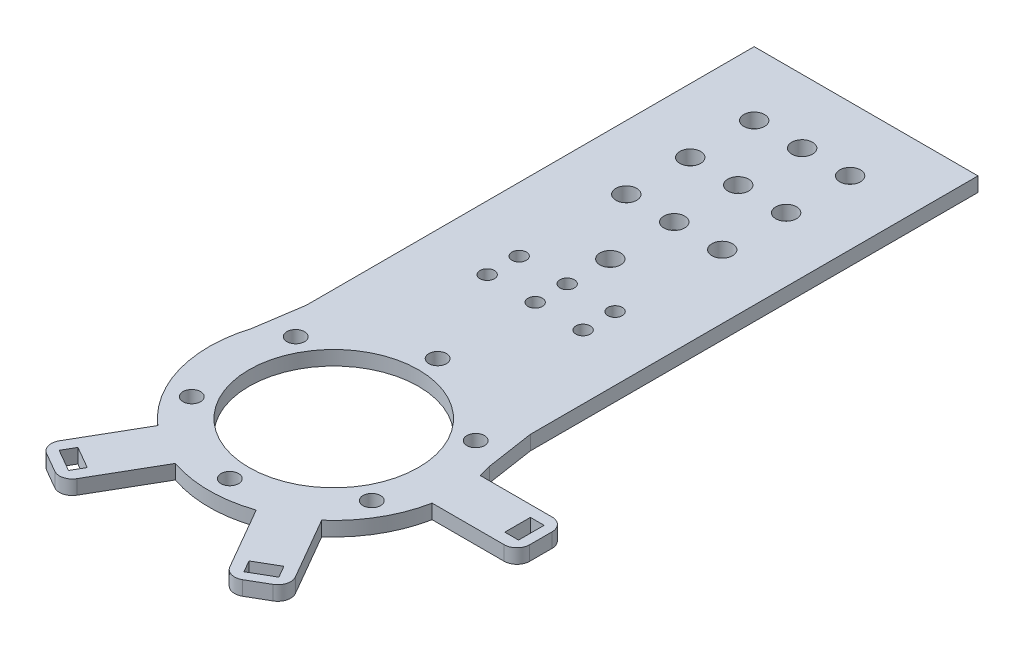
SolidWorks part; units mm, degrees
ref_plane "Front Plane" through (0, 0, 0) normal (0, 0, 1) x (1, 0, 0)
ref_plane "Top Plane" through (0, 0, 0) normal (0, 1, 0) x (1, 0, 0)
ref_plane "Right Plane" through (0, 0, 0) normal (1, 0, 0) x (0, 0, -1)
sketch "Sketch1" plane through (0, 0, 0) normal (0, 1, 0) x (1, 0, 0)
  circle A0 centre (0, 0) radius 45 construction
  circle A1 centre (0, 0) radius 39
  circle A2 centre (0, 0) radius 26.5
  circle A3 centre (0, 0) radius 32.5 construction
  dimension "D1" = 90
  dimension "D2" = 65
  dimension "D3" = 78
  dimension "D4" = 53
extrude "Boss-Extrude1" add sketch "Sketch1" along normal mid plane 4.5
sketch "Sketch3" plane through (0, 0, 0) normal (0, 1, 0) x (1, 0, 0)
  line L0 (0, 0) -> (0, 78) construction
  line L2 (-25, 78) -> (25, 78)
  line L3 (-25, 78) -> (-25, 26.5)
  line L4 (-25, 26.5) -> (25, 26.5)
  line L5 (25, 78) -> (25, 26.5)
  line L6 (0, 26.5) -> (0, 78) construction
  line L7 (-25, 52.25) -> (25, 52.25) construction
  circle A0 centre (0, 0) radius 26.5 construction
  point P3 (0, 52.25)
  dimension "D1" = 78
  dimension "D2" = 50
extrude "Boss-Extrude2" add sketch "Sketch3" along normal mid plane 4.5
sketch "Sketch4" plane through (0, 0, 0) normal (0, 1, 0) x (1, 0, 0)
  line L0 (-25, 53.9666) -> (-37.4668, 10.8276)
  line L1 (-25, 78) -> (-25, 29.9333) construction
  line L2 (-37.4668, 10.8276) -> (-25, 29.9333)
  line L3 (-25, 29.9333) -> (-25, 53.9666)
  line L4 (0, 0) -> (0, 78) construction
  line L5 (25, 78) -> (-25, 78) construction
  line L6 (37.4668, 10.8276) -> (25, 29.9333)
  line L7 (25, 53.9666) -> (37.4668, 10.8276)
  line L8 (25, 29.9333) -> (25, 53.9666)
  circle A0 centre (0, 0) radius 39 construction
extrude "Boss-Extrude3" [suppressed] add sketch "Sketch4" along normal mid plane 4.5
sketch "Sketch6" plane through (0, 0, 0) normal (0, 1, 0) x (1, 0, 0)
  line L0 (0, 0) -> (0, 96.5) construction
  line L1 (-35, 166.5) -> (-35, 26.5)
  line L2 (-35, 166.5) -> (35, 166.5)
  line L4 (35, 166.5) -> (35, 26.5)
  line L5 (0, 26.5) -> (0, 166.5) construction
  line L6 (-35, 96.5) -> (35, 96.5) construction
  line L7 (-35, 26.5) -> (-39, 0)
  line L8 (35, 26.5) -> (39, 0)
  line L9 (39, 0) -> (16.5208, 26.5)
  line L10 (16.5208, 26.5) -> (-14.9815, 26.5)
  line L11 (-14.9815, 26.5) -> (-39, 0)
  circle A0 centre (0, 0) radius 26.5 construction
  circle A1 centre (0, 0) radius 39 construction
  dimension "D1" = 70
  dimension "D2" = 140
extrude "Boss-Extrude4" add sketch "Sketch6" along normal mid plane 4.5
sketch "Sketch2" plane through (0, 0, 0) normal (0, 1, 0) x (1, 0, 0)
  circle A0 centre (0, 0) radius 32.5 construction
  circle A1 centre (0, 32.5) radius 2.75
  dimension "D1" = 65
  dimension "D2" = 5.5
extrude "Cut-Extrude1" cut sketch "Sketch2" against normal through all both and the other way through all contours A1
pattern_circular "CirPattern1" count 6 over 360 about axis through (0, 0, 0) along (0, 1, 0) of "Cut-Extrude1"
sketch "Sketch5" plane through (0, 2.25, 0) normal (0, 1, 0) x (1, 0, 0)
  line L0 (-25, 73) -> (25, 73) construction
  line L4 (35, 166.5) -> (-35, 166.5) construction
  circle A0 centre (0, 73) radius 2.25
  dimension "D1" = 4.5
  dimension "D3" = 93.5
extrude "Cut-Extrude2" cut sketch "Sketch5" against normal through all both and the other way through all
pattern_linear "LPattern1" count 2 spacing 15 along (1, 0, 0) count 2 spacing 10 along (0, 0, 1) of "Cut-Extrude2"
pattern_linear "LPattern2" count 2 spacing 15 along (-1, 0, 0) count 2 spacing 10 along (0, 0, 1) of "Cut-Extrude2"
sketch "Sketch7" plane through (0, 2.25, 0) normal (0, 1, 0) x (1, 0, 0)
  line L0 (0, 0) -> (0, 166.5) construction
  line L1 (35, 166.5) -> (-35, 166.5) construction
  line L2 (-15, 146.5) -> (15, 146.5) construction
  circle A0 centre (-15, 146.5) radius 3.25
  circle A1 centre (15, 146.5) radius 3.25
  point P8 (0, 146.5)
  dimension "D1" = 6.5
  dimension "D2" = 20
  dimension "D3" = 30
extrude "Cut-Extrude3" cut sketch "Sketch7" against normal through all both and the other way through all
pattern_linear "LPattern3" count 3 spacing 20 along (0, 0, 1) of "Cut-Extrude3"
sketch "Sketch8" plane through (0, 2.25, 0) normal (0, 1, 0) x (1, 0, 0)
  line L0 (0, 0) -> (0, 166.5) construction
  line L1 (35, 166.5) -> (-35, 166.5) construction
  circle A0 centre (0, 146.5) radius 3.25
  dimension "D1" = 6.5
  dimension "D2" = 20
extrude "Cut-Extrude4" cut sketch "Sketch8" against normal blind 10
pattern_linear "LPattern4" count 4 spacing 20 along (0, 0, 1) of "Cut-Extrude4"
sketch "Sketch9" plane through (0, 0, 0) normal (0, 1, 0) x (1, 0, 0)
  line L0 (0, 0) -> (59.65, 0) construction
  line L1 (37.8, -7.5) -> (64.8, -7.5)
  line L2 (57.5, -4) -> (61.8, -4)
  line L3 (57.5, -4) -> (57.5, 4)
  line L4 (57.5, 4) -> (61.8, 4)
  line L5 (61.8, -4) -> (61.8, 4)
  line L6 (59.65, 4) -> (59.65, -4) construction
  line L7 (57.5, 0) -> (61.8, 0) construction
  line L8 (37.8, -7.5) -> (37.8, 7.5)
  line L9 (64.8, -7.5) -> (64.8, 7.5)
  line L10 (37.8, 7.5) -> (64.8, 7.5)
  line L11 (37.8, -7.5) -> (64.8, 7.5) construction
  line L12 (64.8, -7.5) -> (37.8, 7.5) construction
  point P8 (51.3, 0)
  dimension "D1" = 4.3
  dimension "D2" = 8
  dimension "D3" = 57.5
  dimension "D4" = 15
  dimension "D5" = 27
  dimension "D6" = 3
extrude "Boss-Extrude5" add sketch "Sketch9" against normal up to surface (2.25 mm away) and the other way up to surface (2.25 mm away) up to face at (0, -2.25, -123.25) other way up to face at (0, 2.25, -123.25)
fillet "Fillet1" radius 4 2 edges at (64.8, 0, -7.5) (64.8, 0, 7.5)
pattern_circular "CirPattern2" count 3 every 60 about axis through (0, 0, 0) along (0, 1, 0) of "Boss-Extrude5", "Fillet1"
